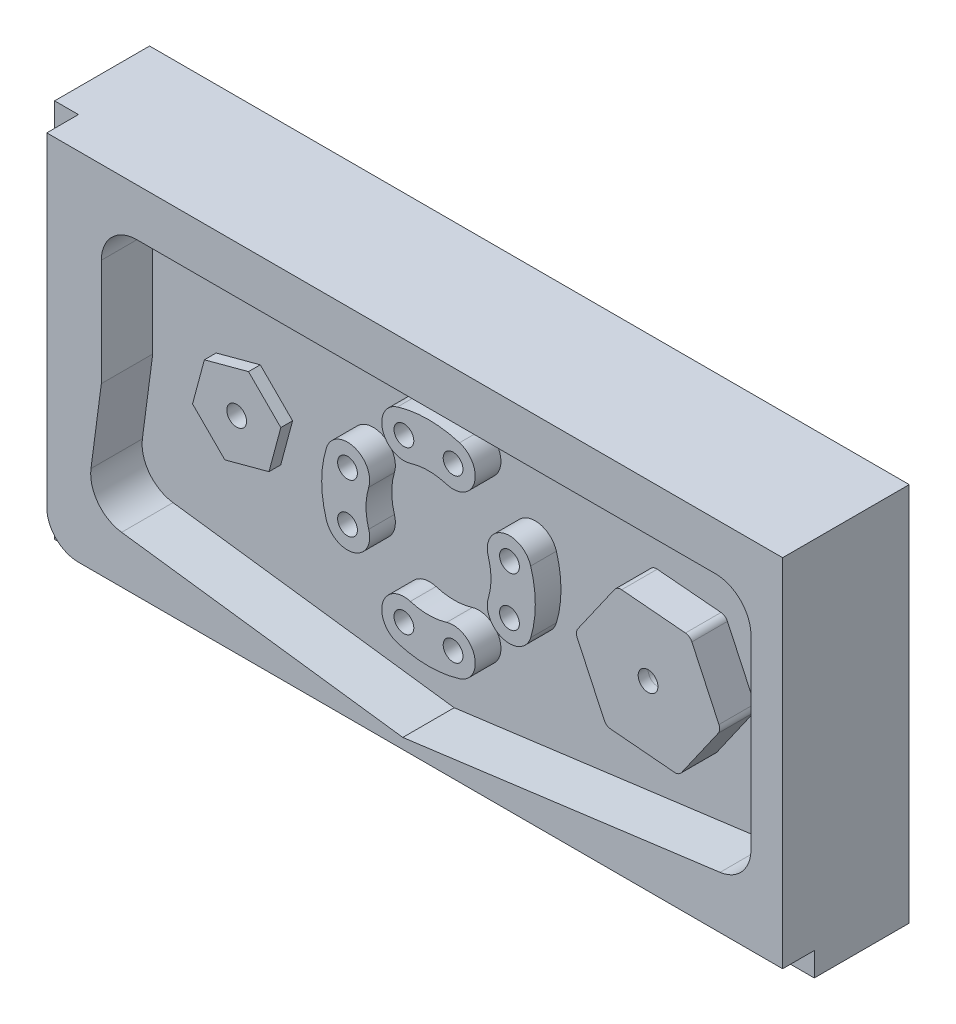
SolidWorks part; units mm, degrees
ref_plane "Front Plane" through (0, 0, 0) normal (0, 0, 1) x (1, 0, 0)
ref_plane "Top Plane" through (0, 0, 0) normal (0, 1, 0) x (1, 0, 0)
ref_plane "Right Plane" through (0, 0, 0) normal (1, 0, 0) x (0, 0, -1)
sketch "Sketch1" plane through (0, 0, 0) normal (0, 0, 1) x (1, 0, 0)
  line L0 (-76.2, 38.1) -> (76.2, 38.1)
  line L1 (-76.2, -38.1) -> (76.2, -38.1)
  line L2 (-76.2, 38.1) -> (-76.2, -38.1)
  line L3 (76.2, 38.1) -> (76.2, -38.1)
  dimension "D1" = 38.1
  dimension "D2" = 38.1
  dimension "D3" = 76.2
  dimension "D4" = 76.2
extrude "Boss-Extrude1" add sketch "Sketch1" along normal blind 25.4
sketch "Sketch2" plane through (0, 0, 25.4) normal (0, 0, 1) x (1, 0, 0)
  line L0 (76.2, 38.1) -> (-76.2, 38.1) construction
  line L1 (-71.4248, 38.1) -> (76.2, 38.1)
  line L2 (-71.4248, 38.1) -> (-71.4248, -26.9748)
  line L3 (-65.0748, -33.3248) -> (76.2, -33.3248)
  line L4 (76.2, 38.1) -> (76.2, -33.3248)
  line L5 (-71.4248, 38.1) -> (76.2, -33.3248) construction
  line L6 (-71.4248, -33.3248) -> (76.2, 38.1) construction
  line L7 (-76.2, -38.1) -> (76.2, -38.1) construction
  line L8 (76.2, -38.1) -> (76.2, 38.1) construction
  line L9 (-76.2, 38.1) -> (-76.2, -38.1) construction
  arc A0 (-65.0748, -33.3248) -> (-71.4248, -26.9748) centre (-65.0748, -26.9748) cw
  point P0 (0, 0)
  dimension "D4" = 6.35
  dimension "D1" = 0
  dimension "D2" = 4.7752
  dimension "D3" = 0
  dimension "D5" = 4.7752
extrude "Cut-Extrude1" cut sketch "Sketch2" against normal blind 6.35 flip side to cut
sketch "Sketch5" plane through (0, 0, 25.4) normal (0, 0, 1) x (1, 0, 0)
  line L0 (-53.34, 28.575) -> (62.7126, 28.575)
  line L1 (69.85, 21.4376) -> (69.85, -15.7691)
  line L2 (0, -31.2244) -> (63.6442, -22.8455)
  line L3 (0, -31.2244) -> (-56.4114, -23.7977)
  line L4 (-60.4774, 0) -> (-62.5562, -15.7897)
  line L5 (-60.4774, 0) -> (-60.4774, 21.4376)
  line L6 (76.2, -33.3248) -> (76.2, 38.1) construction
  line L11 (-71.4248, 38.1) -> (-71.4248, -26.9748) construction
  line L12 (76.2, 38.1) -> (-71.4248, 38.1) construction
  arc A0 (-56.4114, -23.7977) -> (-62.5562, -15.7897) centre (-55.4798, -16.7213) cw
  arc A1 (-60.4774, 21.4376) -> (-53.34, 28.575) centre (-53.34, 21.4376) cw
  arc A2 (62.7126, 28.575) -> (69.85, 21.4376) centre (62.7126, 21.4376) cw
  arc A3 (69.85, -15.7691) -> (63.6442, -22.8455) centre (62.7126, -15.7691) cw
  dimension "D1" = 10.9474
  dimension "D3" = 7.1374
  dimension "D4" = 7.1374
  dimension "D2" = 9.525
  dimension "D7" = 6.35
  dimension "D8" = 90
extrude "Cut-Extrude3" cut sketch "Sketch5" against normal blind 10.3124
sketch "Sketch6" plane through (0, 0, 15.0876) normal (0, 0, 1) x (1, 0, 0)
  arc A0 (-20.501, 6.2238) -> (-20.501, -6.2238) centre (0, 0) ccw
  arc A1 (-11.9944, 3.6413) -> (-11.9944, -3.6413) centre (0, 0) ccw
  arc A2 (20.501, -6.2238) -> (20.501, 6.2238) centre (0, 0) ccw
  arc A3 (-6.2238, -20.501) -> (6.2238, -20.501) centre (0, 0) ccw
  arc A4 (6.2238, 20.501) -> (-6.2238, 20.501) centre (0, 0) ccw
  arc A5 (3.6413, 11.9944) -> (-3.6413, 11.9944) centre (0, 0) ccw
  arc A6 (11.9944, -3.6413) -> (11.9944, 3.6413) centre (0, 0) ccw
  arc A7 (-3.6413, -11.9944) -> (3.6413, -11.9944) centre (0, 0) ccw
  arc A8 (-6.2238, 20.501) -> (-3.6413, 11.9944) centre (-4.9326, 16.2477) ccw
  arc A9 (3.6413, 11.9944) -> (6.2238, 20.501) centre (4.9326, 16.2477) ccw
  arc A10 (20.501, 6.2238) -> (11.9944, 3.6413) centre (16.2477, 4.9326) ccw
  arc A11 (11.9944, -3.6413) -> (20.501, -6.2238) centre (16.2477, -4.9326) ccw
  arc A12 (-3.6413, -11.9944) -> (-6.2238, -20.501) centre (-4.9326, -16.2477) ccw
  arc A13 (6.2238, -20.501) -> (3.6413, -11.9944) centre (4.9326, -16.2477) ccw
  arc A14 (-20.501, -6.2238) -> (-11.9944, -3.6413) centre (-16.2477, -4.9326) ccw
  arc A15 (-11.9944, 3.6413) -> (-20.501, 6.2238) centre (-16.2477, 4.9326) ccw
  point P4 (-19.2453, 19.2453)
  point P6 (2.5145, 2.5145)
  point P7 (19.5534, 19.5534)
  point P9 (-19.5839, -19.5839)
  point P11 (19.3126, -19.3126)
  point P13 (-16.7309, 21.7598)
  point P14 (-2.5145, -2.5145)
  point P15 (-21.7598, 16.7309)
  point P17 (16.7982, -21.8271)
  point P19 (21.8271, -16.7982)
  point P20 (2.5145, -2.5145)
  point P21 (22.0679, 17.039)
  point P22 (-2.5145, 2.5145)
  point P23 (17.039, 22.0679)
  point P25 (-22.0983, -17.0694)
  point P27 (-17.0694, -22.0983)
  dimension "D1" = 42.8498
  dimension "D2" = 25.0698
extrude "Boss-Extrude3" add sketch "Sketch6" along normal blind 5.1562
sketch "Sketch11" plane through (0, 0, 15.0876) normal (0, 0, 1) x (1, 0, 0)
  line L0 (-71.4248, 38.1) -> (-71.4248, -26.9748) construction
  line L1 (-38.9028, 8.9025) -> (-47.7559, 6.5303)
  line L2 (-47.7559, 6.5303) -> (-50.1281, -2.3228)
  line L3 (-50.1281, -2.3228) -> (-43.6472, -8.8037)
  line L4 (-43.6472, -8.8037) -> (-34.794, -6.4315)
  line L5 (-34.794, -6.4315) -> (-32.4218, 2.4216)
  line L6 (-32.4218, 2.4216) -> (-38.9028, 8.9025)
  circle A0 centre (-41.275, 0.0494) radius 7.9375 construction
  circle A1 centre (-41.275, 0.0494) radius 1.9812
  dimension "D4" = 3.9624
  dimension "D1" = 15.875
  dimension "D2" = 15
  dimension "D3" = 41.275
extrude "Boss-Extrude4" add sketch "Sketch11" along normal blind 2.3622
sketch "Sketch12" plane through (0, 0, 15.0876) normal (0, 0, 1) x (1, 0, 0)
  line L0 (76.2, -33.3248) -> (76.2, 38.1) construction
  line L1 (52.7439, -12.5459) -> (60.1122, -2.0229)
  line L2 (60.2494, -0.4541) -> (54.8204, 11.1886)
  line L3 (53.5304, 12.0919) -> (40.733, 13.2115)
  line L4 (39.3057, 12.5459) -> (31.9374, 2.0229)
  line L5 (31.8002, 0.4541) -> (37.2292, -11.1886)
  line L6 (38.5192, -12.0919) -> (51.3166, -13.2115)
  circle A0 centre (46.0248, 0) radius 12.7 construction
  arc A1 (53.5304, 12.0919) -> (54.8204, 11.1886) centre (53.3931, 10.5231) cw
  arc A2 (60.2494, -0.4541) -> (60.1122, -2.0229) centre (58.8222, -1.1196) cw
  arc A3 (52.7439, -12.5459) -> (51.3166, -13.2115) centre (51.4539, -11.6427) cw
  arc A4 (38.5192, -12.0919) -> (37.2292, -11.1886) centre (38.6565, -10.5231) cw
  arc A5 (31.8002, 0.4541) -> (31.9374, 2.0229) centre (33.2274, 1.1196) cw
  arc A6 (39.3057, 12.5459) -> (40.733, 13.2115) centre (40.5957, 11.6427) cw
  circle A7 centre (46.0248, 0) radius 1.9812
  dimension "D4" = 1.5748
  dimension "D5" = 3.9624
  dimension "D1" = 25.4
  dimension "D2" = 35
  dimension "D3" = 46.0248
extrude "Boss-Extrude5" add sketch "Sketch12" along normal blind 7.1374
hole_wizard "5/32 (0.15625) Diameter Hole1" positions "Sketch10" profile "Sketch9" hole size "5/32" standard "Ansi Inch"
sketch "Sketch10" plane through (0, 0, 20.2438) normal (0, 0, 1) x (1, 0, 0)
  arc A0 (-11.9944, 3.6413) -> (-20.501, 6.2238) centre (-16.2477, 4.9326) ccw construction
  point P0 (-16.2477, 4.9326)
  point P1 (-16.2477, -4.9326)
  point P4 (-4.9326, -16.2477)
  point P7 (4.9326, -16.2477)
  point P10 (16.2477, -4.9326)
  point P13 (16.2477, 4.9326)
  point P16 (4.9326, 16.2477)
  point P19 (-4.9326, 16.2477)
  point P26 (-41.275, 0.0494)
  point P29 (46.0248, 0)
  dimension "D1" = 0
sketch "Sketch9" plane through (-16.2477, 4.9326, 20.2438) normal (1, 0, 0) x (0, -1, 0)
  line L0 (0, 0) -> (0, 20.2438)
  line L1 (0, 20.2438) -> (1.9844, 20.2438)
  line L2 (1.9844, 20.2438) -> (1.9844, 0)
  line L5 (1.9844, 0) -> (0, 0)
  line L11 (0, -6.35) -> (0, 107.95) construction
  dimension "Thru Hole Dia." = 3.9688
  dimension "Thru Hole Depth" = 20.2438
